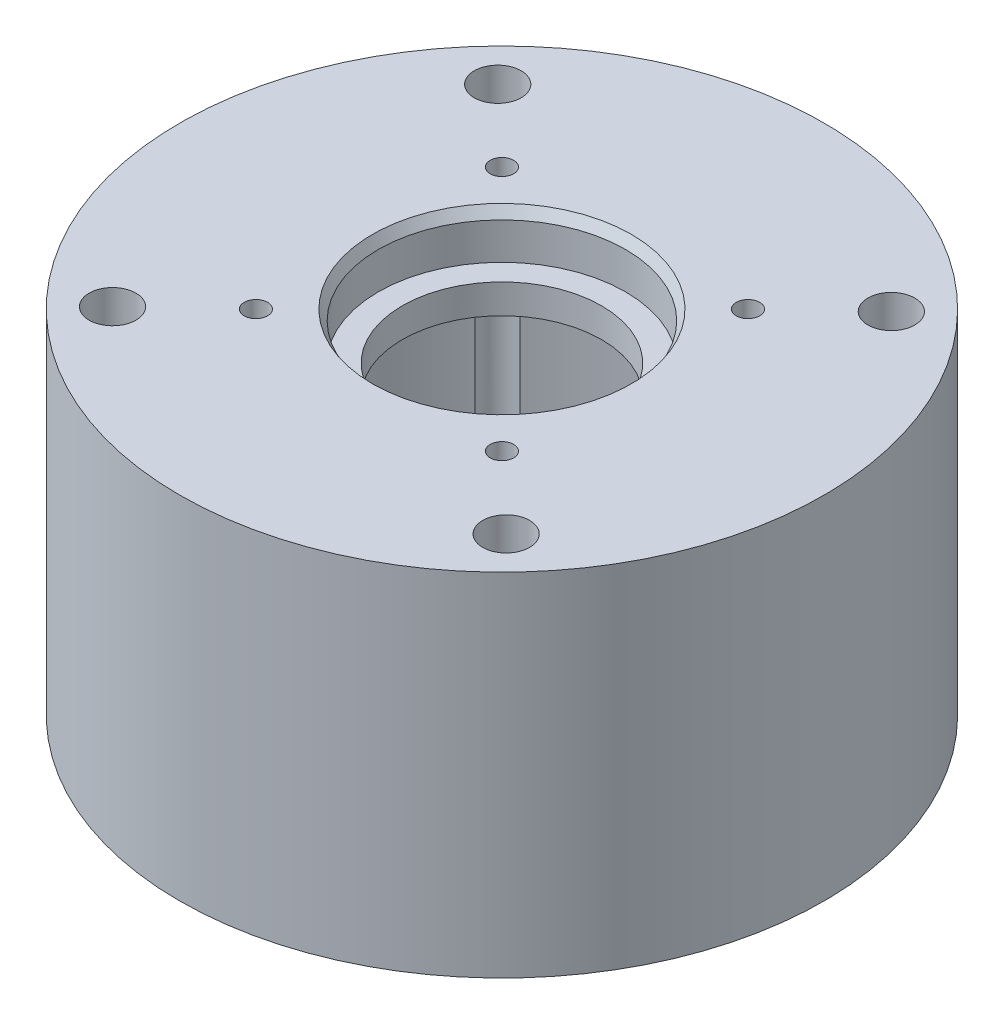
SolidWorks part; units mm, degrees
ref_plane "Спереди" through (0, 0, 0) normal (0, 0, 1) x (1, 0, 0)
ref_plane "Сверху" through (0, 0, 0) normal (0, 1, 0) x (1, 0, 0)
ref_plane "Справа" through (0, 0, 0) normal (1, 0, 0) x (0, 0, -1)
sketch "Эскиз1" plane through (0, 0, 0) normal (0, 1, 0) x (1, 0, 0)
  circle A0 centre (0, 0) radius 55
  dimension "D1" = 110
extrude "Бобышка-Вытянуть1" add sketch "Эскиз1" along normal blind 60
sketch "Эскиз2" plane through (0, 0, 0) normal (0, -1, 0) x (1, 0, 0)
  circle A0 centre (0, 0) radius 50
  dimension "D1" = 100
extrude "Вырез-Вытянуть1" cut sketch "Эскиз2" against normal blind 47
sketch "Эскиз3" plane through (0, 47, 0) normal (0, -1, 0) x (1, 0, 0)
  line L1 (-16.75, -7.7) -> (16.75, -7.7) construction
  line L2 (-16.75, -7.7) -> (-16.75, 7.7) construction
  line L3 (-16.75, 7.7) -> (16.75, 7.7) construction
  line L4 (16.75, -7.7) -> (16.75, 7.7) construction
  line L5 (-16.75, -7.7) -> (16.75, 7.7) construction
  line L6 (-16.75, 7.7) -> (16.75, -7.7) construction
  circle A0 centre (0, 0) radius 17
  point P0 (0, 0)
  dimension "D1" = 15.4
  dimension "D3" = 34
  dimension "D2" = 33.5
extrude "Вырез-Вытянуть2" cut sketch "Эскиз3" against normal through all
sketch "Эскиз4" plane through (0, 60, 0) normal (0, 1, 0) x (1, 0, 0)
  line L7 (23.35, 22.85) -> (23.35, -22.85) construction
  line L8 (39.3095, -38.4677) -> (-39.3095, 38.4677) construction
  line L9 (23.35, -22.85) -> (-23.35, -22.85) construction
  line L10 (-23.35, -22.85) -> (-23.35, 22.85) construction
  line L13 (23.35, -22.85) -> (-23.35, 22.85) construction
  line L15 (39.3095, 38.4677) -> (-39.3095, -38.4677) construction
  line L16 (23.35, 22.85) -> (-23.35, -22.85) construction
  circle A4 centre (0, 0) radius 55 construction
  circle A5 centre (33.5917, -32.8724) radius 4
  circle A6 centre (-33.5917, -32.8724) radius 4
  circle A7 centre (-33.5917, 32.8724) radius 4
  circle A8 centre (33.5917, 32.8724) radius 4
  point P0 (0, 0)
  point P5 (0, 0)
  dimension "D4" = 8
  dimension "D1" = 46.7
  dimension "D5" = 8
  dimension "D6" = 8
  dimension "D7" = 8
  dimension "D8" = 8
  dimension "D9" = 45.7
extrude "Вырез-Вытянуть3" cut sketch "Эскиз4" against normal through all
sketch "Sketch1" plane through (0, 60, 0) normal (0, 1, 0) x (1, 0, 0)
  circle A0 centre (0, 0) radius 21.1
  dimension "D1" = 42.2
extrude "Cut-Extrude1" cut sketch "Sketch1" against normal blind 8
chamfer "Chamfer1" distance 1 angle 60 1 edges at (0, 60, 21.1)
sketch "Sketch2" plane through (0, 60, 0) normal (0, 1, 0) x (1, 0, 0)
  line L1 (21, -21) -> (-21, -21) construction
  line L2 (21, -21) -> (21, 21) construction
  line L3 (21, 21) -> (-21, 21) construction
  line L4 (-21, -21) -> (-21, 21) construction
  line L5 (21, -21) -> (-21, 21) construction
  line L6 (21, 21) -> (-21, -21) construction
  circle A0 centre (21, 21) radius 2
  circle A1 centre (-21, 21) radius 2
  circle A2 centre (21, -21) radius 2
  circle A3 centre (-21, -21) radius 2
  point P0 (0, 0)
  dimension "D2" = 4
  dimension "D1" = 42
extrude "Cut-Extrude2" cut sketch "Sketch2" against normal through all
sketch "Sketch3" plane through (0, 47, 0) normal (0, -1, 0) x (1, 0, 0)
  line L1 (-21, -16.9) -> (-24.5507, -18.95)
  line L2 (-24.5507, -18.95) -> (-24.5507, -23.05)
  line L3 (-24.5507, -23.05) -> (-21, -25.1)
  line L4 (-21, -25.1) -> (-17.4493, -23.05)
  line L5 (-17.4493, -23.05) -> (-17.4493, -18.95)
  line L6 (-17.4493, -18.95) -> (-21, -16.9)
  line L7 (-21, 25.1) -> (-24.5507, 23.05)
  line L8 (-24.5507, 23.05) -> (-24.5507, 18.95)
  line L9 (-24.5507, 18.95) -> (-21, 16.9)
  line L10 (-21, 16.9) -> (-17.4493, 18.95)
  line L11 (-17.4493, 18.95) -> (-17.4493, 23.05)
  line L12 (-17.4493, 23.05) -> (-21, 25.1)
  line L13 (24.5507, 23.05) -> (21, 25.1)
  line L14 (21, 25.1) -> (17.4493, 23.05)
  line L15 (17.4493, 23.05) -> (17.4493, 18.95)
  line L16 (17.4493, 18.95) -> (21, 16.9)
  line L17 (21, 16.9) -> (24.5507, 18.95)
  line L18 (24.5507, 18.95) -> (24.5507, 23.05)
  line L19 (24.5507, -18.95) -> (21, -16.9)
  line L20 (21, -16.9) -> (17.4493, -18.95)
  line L21 (17.4493, -18.95) -> (17.4493, -23.05)
  line L22 (17.4493, -23.05) -> (21, -25.1)
  line L23 (21, -25.1) -> (24.5507, -23.05)
  line L24 (24.5507, -23.05) -> (24.5507, -18.95)
  circle A0 centre (-21, -21) radius 4.1 construction
  circle A1 centre (-21, 21) radius 4.1 construction
  circle A2 centre (21, 21) radius 4.1 construction
  circle A3 centre (21, -21) radius 4.1 construction
  dimension "D1" = 8.2
extrude "Cut-Extrude3" cut sketch "Sketch3" against normal blind 4
